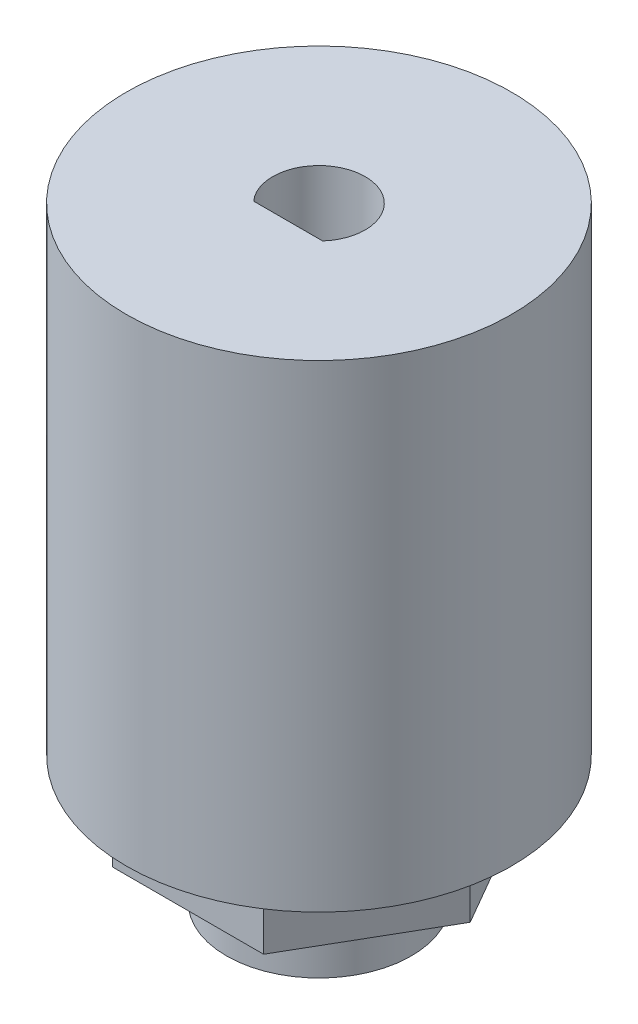
SolidWorks part; units mm, degrees
ref_plane "Front Plane" through (0, 0, 0) normal (0, 0, 1) x (1, 0, 0)
ref_plane "Top Plane" through (0, 0, 0) normal (0, 1, 0) x (1, 0, 0)
ref_plane "Right Plane" through (0, 0, 0) normal (1, 0, 0) x (0, 0, -1)
sketch "Sketch1" plane through (0, 0, 0) normal (0, 1, 0) x (1, 0, 0)
  circle A0 centre (0, 0) radius 6
  dimension "D1" = 12
extrude "Boss-Extrude1" add sketch "Sketch1" along normal blind 3.8
sketch "Sketch2" plane through (0, 3.8, 0) normal (0, 1, 0) x (1, 0, 0)
  line L1 (9.815, 0) -> (4.9075, 8.5)
  line L2 (4.9075, 8.5) -> (-4.9075, 8.5)
  line L3 (-4.9075, 8.5) -> (-9.815, 0)
  line L4 (-9.815, 0) -> (-4.9075, -8.5)
  line L5 (-4.9075, -8.5) -> (4.9075, -8.5)
  line L6 (4.9075, -8.5) -> (9.815, 0)
  circle A0 centre (0, 0) radius 8.5 construction
  dimension "D1" = 17
extrude "Boss-Extrude2" add sketch "Sketch2" along normal blind 4.5
sketch "Sketch3" plane through (0, 8.3, 0) normal (0, 1, 0) x (1, 0, 0)
  circle A0 centre (0, 0) radius 12.5
  dimension "D1" = 25
extrude "Boss-Extrude3" add sketch "Sketch3" along normal blind 4
sketch "Sketch4" plane through (0, 12.3, 0) normal (0, 1, 0) x (1, 0, 0)
  circle A0 centre (0, 0) radius 12.5
  dimension "D1" = 25
extrude "Boss-Extrude4" add sketch "Sketch4" along normal blind 27
sketch "Sketch5" plane through (0, 39.3, 0) normal (0, 1, 0) x (1, 0, 0)
  line L0 (-2.2361, -2) -> (2.2361, -2)
  circle A0 centre (0, 0) radius 3
  point P3 (0, 3)
  dimension "D1" = 6
  dimension "D2" = 5
extrude "Cut-Extrude1" cut sketch "Sketch5" against normal through all contours L0 A0
sketch "Sketch6" plane through (0, 0, 0) normal (0, -1, 0) x (1, 0, 0)
  circle A0 centre (0, 0) radius 3.6
  dimension "D1" = 7.2
extrude "Cut-Extrude2" cut sketch "Sketch6" against normal blind 6
